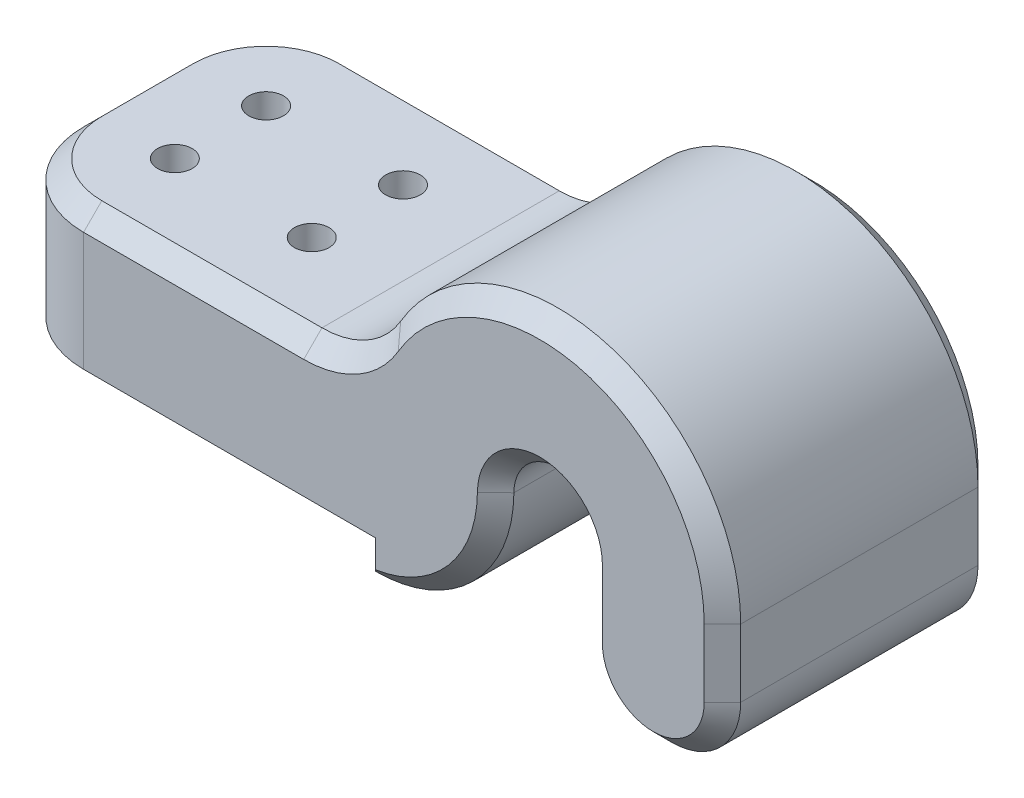
SolidWorks part; units mm, degrees
ref_plane "Front Plane" through (0, 0, 0) normal (0, 0, 1) x (1, 0, 0)
ref_plane "Top Plane" through (0, 0, 0) normal (0, 1, 0) x (1, 0, 0)
ref_plane "Right Plane" through (0, 0, 0) normal (1, 0, 0) x (0, 0, -1)
sketch "Sketch1" plane through (0, 0, 0) normal (0, 0, 1) x (1, 0, 0)
  line L0 (0, 3.175) -> (0, 0)
  line L2 (0, 3.175) -> (-40, 3.175)
  line L4 (24.85, 15) -> (24.85, 7.575)
  line L5 (40, 7.575) -> (40, 15)
  line L7 (-5.8789, 20.175) -> (-40, 20.175)
  line L8 (-40, 20.175) -> (-40, 3.175)
  line L11 (9.893, 0) -> (0, 0) construction
  line L13 (0, 0) -> (-12.6509, 0) construction
  arc A0 (0, 0) -> (15.1501, 15.0365) centre (0, 15.1506) ccw
  arc A1 (15.1501, 15.0365) -> (24.85, 15) centre (20, 15) cw
  arc A2 (24.85, 7.575) -> (40, 7.575) centre (32.425, 7.575) ccw
  arc A3 (40, 15) -> (2.7474, 25.1167) centre (20, 15) ccw
  arc A7 (2.7474, 25.1167) -> (-5.8789, 20.175) centre (-5.8789, 30.175) cw
  dimension "D1" = 15
  dimension "D6" = 4.85
  dimension "D7" = 10
  dimension "D2" = 20
  dimension "D3" = 3.175
  dimension "D4" = 17
  dimension "D5" = 40
extrude "Boss-Extrude1" add sketch "Sketch1" along normal blind 30
fillet "Fillet1" radius 10 2 edges at (-40, 11.675, 0) (-40, 11.675, 30)
chamfer "Chamfer1" distance 2 angle 45 26 edges at (-40, 3.175, 15) (-37.0711, 3.175, 27.0711) (-37.0711, 3.175, 2.9289) (-15, 3.175, 30) (0, 1.5875, 30) (10.6727, 4.3972, 30) (20.0183, 19.85, 30) (24.85, 11.2875, 30) (32.425, 0, 30) (40, 11.2875, 30) (25.2415, 34.3009, 30) (-17.9395, 20.175, 30) (-37.0711, 20.175, 27.0711) (-40, 20.175, 15) (-37.0711, 20.175, 2.9289) (-17.9395, 20.175, 0) (25.2415, 34.3009, 0) (40, 11.2875, 0) (32.425, 0, 0) (24.85, 11.2875, 0) (20.0183, 19.85, 0) (10.6727, 4.3972, 0) (0, 1.5875, 0) (-15, 3.175, 0) (-0.9082, 21.4979, 30) (-0.9082, 21.4979, 0)
sketch "Sketch3" plane through (0, 3.175, 0) normal (0, -1, 0) x (1, 0, 0)
  line L0 (-38, 15) -> (-11.1185, 15) construction
  line L1 (-38, 20) -> (-38, 10) construction
  circle A0 centre (-30, 20) radius 1.9
  circle A1 centre (-15, 20) radius 1.9
  circle A2 centre (-15, 10) radius 1.9
  circle A3 centre (-30, 10) radius 1.9
  arc A4 (-30, 30) -> (-40, 20) centre (-30, 20) ccw construction
  dimension "D1" = 3.8
  dimension "D2" = 15
extrude "Cut-Extrude1" cut sketch "Sketch3" against normal through all
chamfer "Chamfer2" distance 2 angle 10 4 edges at (-28.1, 3.175, 20) (-28.1, 3.175, 10) (-13.1, 3.175, 10) (-13.1, 3.175, 20)
